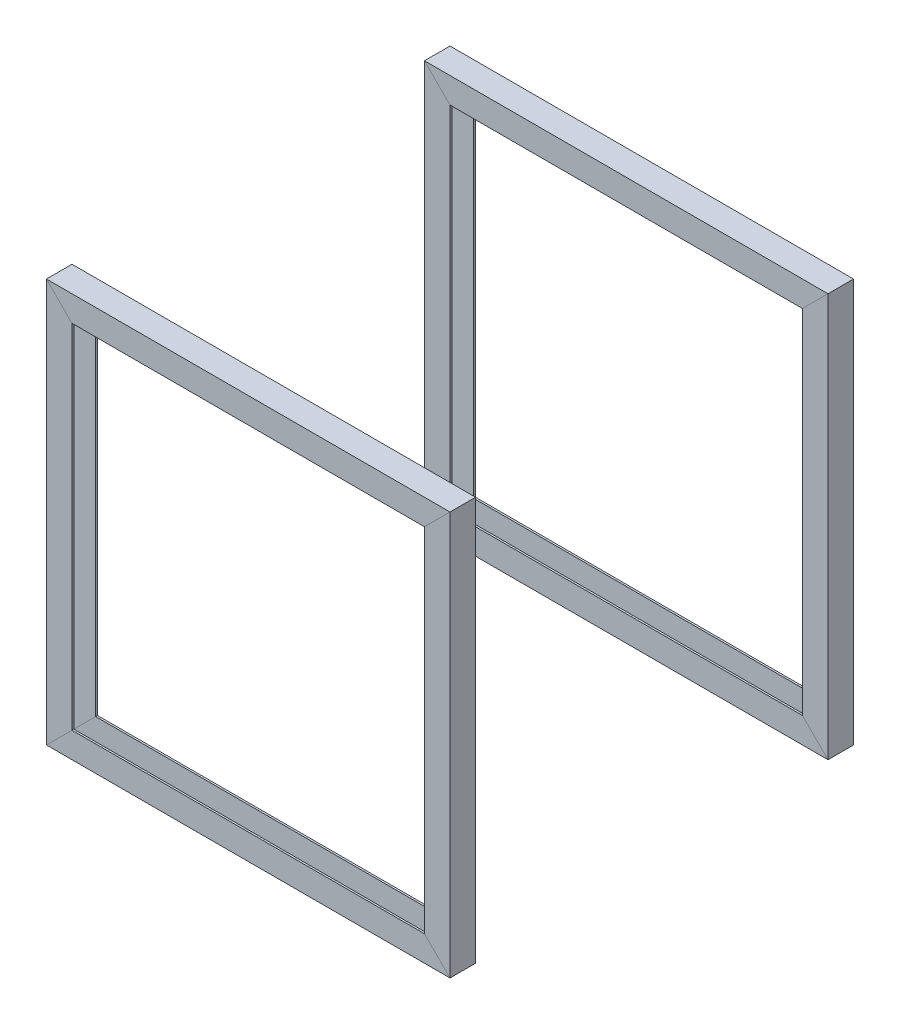
SolidWorks part; units mm, degrees
ref_plane "Front Plane" through (0, 0, 0) normal (0, 0, 1) x (1, 0, 0)
ref_plane "Top Plane" through (0, 0, 0) normal (0, 1, 0) x (1, 0, 0)
ref_plane "Right Plane" through (0, 0, 0) normal (1, 0, 0) x (0, 0, -1)
sketch "Sketch1" plane through (0, 0, 0) normal (0, 0, 1) x (1, 0, 0)
  line L1 (-75, 75) -> (75, 75)
  line L2 (-75, 75) -> (-75, -75)
  line L3 (-75, -75) -> (75, -75)
  line L4 (75, 75) -> (75, -75)
  line L5 (-75, 75) -> (75, -75) construction
  line L6 (-75, -75) -> (75, 75) construction
  point P0 (0, 0)
  dimension "D1" = 150
  dimension "D2" = 150
other "C channel 80 X 8(1)"
ref_plane "Plane1" through (-75, 75, 0) normal (1, 0, 0) x (0, 1, 0)
sketch "Sketch11" plane through (-75, 75, 0) normal (1, 0, 0) x (0, 1, 0)
  line L0 (0, 0) -> (0, -9.5)
  line L1 (0, -9.5) -> (-9.5, -9.5)
  line L2 (0, 0) -> (-9.5, 0)
  line L3 (0, 0) -> (-150, 0) construction
  line L4 (-0.7, -0.7) -> (-9.5, -0.7)
  line L5 (-0.7, -0.7) -> (-0.7, -8.8)
  line L6 (-0.7, -8.8) -> (-9.5, -8.8)
  line L7 (-9.5, 0) -> (-9.5, -0.7)
  line L8 (-9.5, -9.5) -> (-9.5, -8.8)
  dimension "D2" = 9.5
  dimension "D1" = 0.7
  dimension "D3" = 9.5
ref_plane "Plane2" through (0, 0, -75) normal (0, 0, 1) x (1, 0, 0)
mirror "Mirror1" about plane through (0, 0, -75) normal (0, 0, 1) of bodies 103 104 102 101
